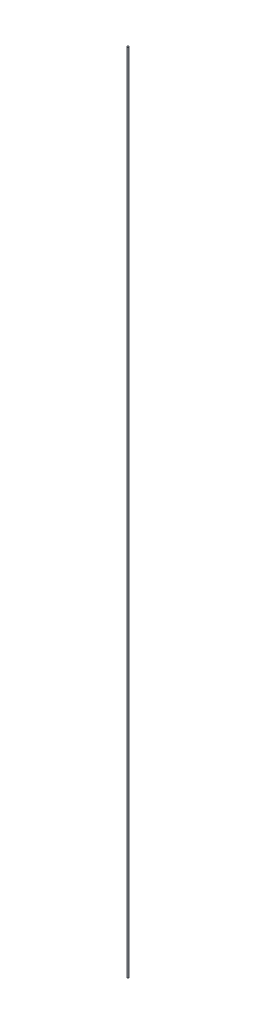
SolidWorks part; units mm, degrees
ref_plane "Front Plane" through (0, 0, 0) normal (0, 0, 1) x (1, 0, 0)
ref_plane "Top Plane" through (0, 0, 0) normal (0, 1, 0) x (1, 0, 0)
ref_plane "Right Plane" through (0, 0, 0) normal (1, 0, 0) x (0, 0, -1)
sketch "草图1" plane through (0, 0, 0) normal (0, 1, 0) x (1, 0, 0)
  circle A0 centre (0, 0) radius 1
extrude "凸台-拉伸1" add sketch "草图1" along normal blind 1000
sketch "草图2" plane through (0, 1000, 0) normal (0, 1, 0) x (1, 0, 0)
  point P0 (0, 0)
sketch "草图3" plane through (0, 0, 0) normal (0, -1, 0) x (1, 0, 0)
  point P0 (0, 0)
